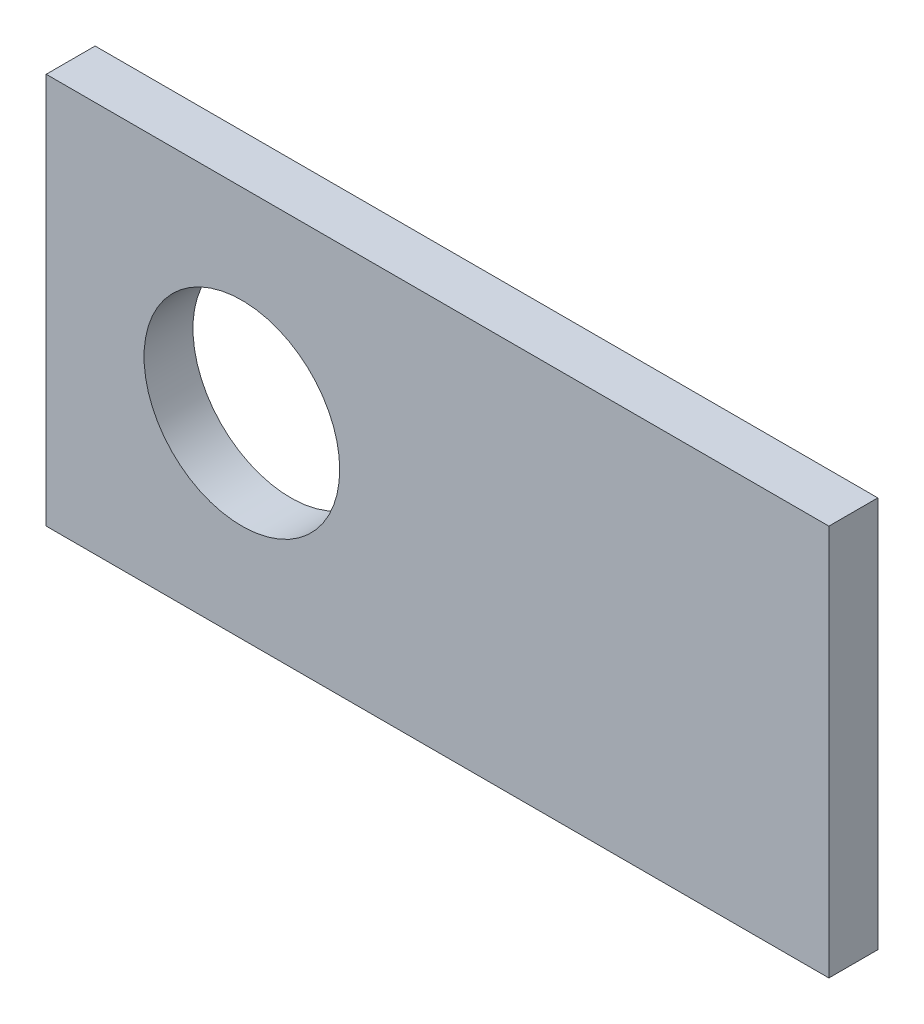
SolidWorks part; units mm, degrees
ref_plane "Front" through (0, 0, 0) normal (0, 0, 1) x (1, 0, 0)
ref_plane "Top" through (0, 0, 0) normal (0, 1, 0) x (1, 0, 0)
ref_plane "Right" through (0, 0, 0) normal (1, 0, 0) x (0, 0, -1)
sketch "Sketch1" plane through (0, 0, 0) normal (0, 0, 1) x (1, 0, 0)
  line L1 (0, 0) -> (50.8, 0)
  line L2 (0, 0) -> (0, 25.4)
  line L3 (0, 25.4) -> (50.8, 25.4)
  line L4 (50.8, 0) -> (50.8, 25.4)
  line L5 (0, 0) -> (50.8, 25.4) construction
  line L6 (0, 25.4) -> (50.8, 0) construction
  circle A0 centre (12.7, 12.7) radius 6.35
  point P4 (25.4, 12.7)
  dimension "D3" = 12.7
  dimension "D1" = 25.4
  dimension "D2" = 50.8
  dimension "D4" = 38.1
extrude "Boss-Extrude1" add sketch "Sketch1" along normal blind 3.175
